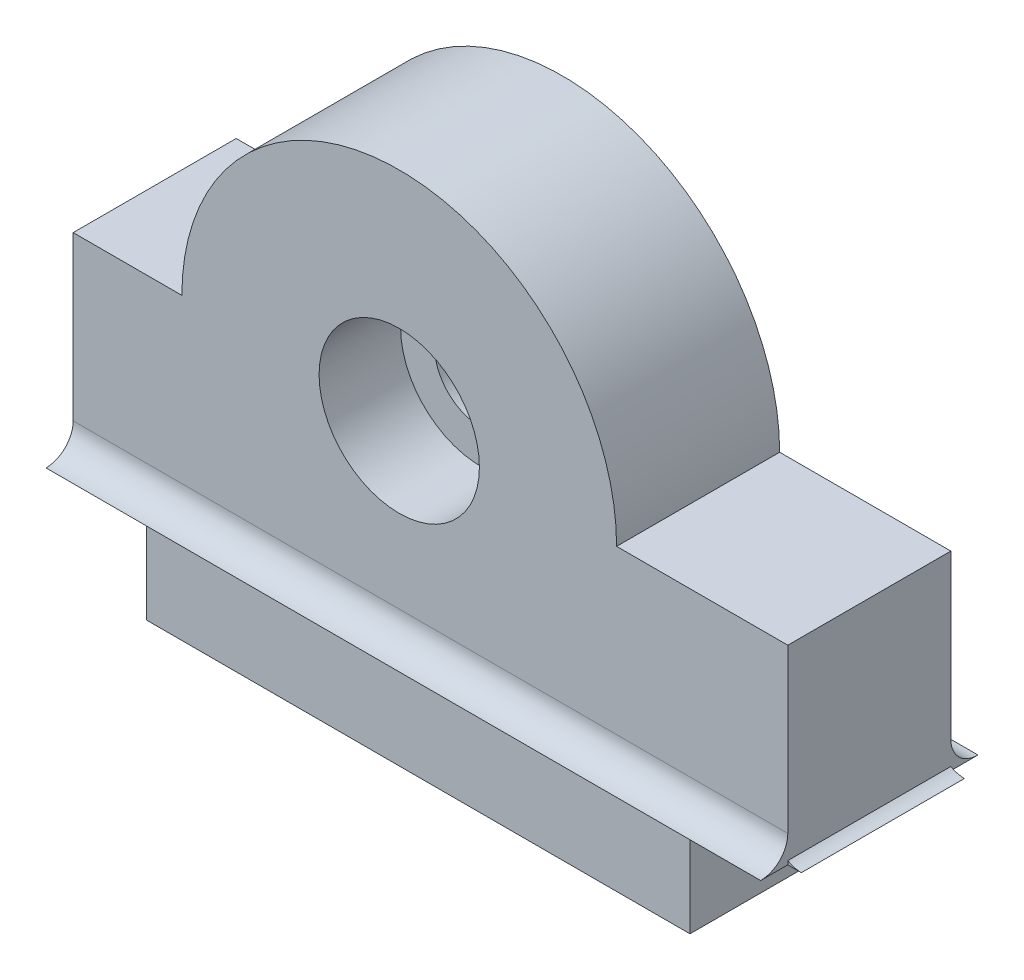
SolidWorks part; units mm, degrees
ref_plane "Front Plane" through (0, 0, 0) normal (0, 0, 1) x (1, 0, 0)
ref_plane "Top Plane" through (0, 0, 0) normal (0, 1, 0) x (1, 0, 0)
ref_plane "Right Plane" through (0, 0, 0) normal (1, 0, 0) x (0, 0, -1)
sketch "Sketch1" plane through (0, 0, 0) normal (0, 0, 1) x (1, 0, 0)
  line L0 (0, 0) -> (20, 0)
  line L1 (0, 0) -> (0, 4)
  line L2 (20, 0) -> (20, 4)
  line L3 (0, 4) -> (-2.7, 4)
  line L4 (23.6, 11) -> (23.6, 4)
  line L5 (-2.7, 4) -> (-2.7, 11)
  line L6 (-2.7, 11) -> (1.3, 11)
  line L7 (17.3, 11) -> (23.6, 11)
  line L8 (23.6, 4) -> (20, 4)
  line L9 (1.3, 11) -> (9.3, 11) construction
  line L10 (12.9373, 11) -> (9.3, 11) construction
  arc A0 (17.3, 11) -> (1.3, 11) centre (9.3, 11) ccw
  circle A1 centre (9.3, 11) radius 2.95
  point P19 (10, 0)
  point P22 (9.3, 11)
  dimension "D1" = 7
  dimension "D5" = 9.3
  dimension "D6" = 20
  dimension "D2" = 8
  dimension "D4" = 5.9
  dimension "D3" = 2.7
  dimension "D7" = 23.6
  dimension "D9" = 4
extrude "Boss-Extrude1" add sketch "Sketch1" along normal blind 6
sketch "Sketch2" plane through (-2.7, 0, 0) normal (-1, 0, 0) x (0, 0, 1)
  line L0 (3, 0) -> (3, 7) construction
  line L1 (6, 4) -> (6, 5)
  line L2 (6, 4) -> (7, 4)
  line L3 (0, 4) -> (-1, 4)
  line L4 (0, 4) -> (0, 5)
  arc A0 (6, 5) -> (7, 4) centre (7, 5) ccw
  arc A1 (0, 5) -> (-1, 4) centre (-1, 5) cw
  dimension "D1" = 1
  dimension "D2" = 1
  dimension "D3" = 6
  dimension "D4" = 3
  dimension "D5" = 4
extrude "Boss-Extrude2" add sketch "Sketch2" against normal up to surface (26.3 mm away) up to face at (23.6, 7.5, 3)
sketch "Sketch4" plane through (0, 0, 6) normal (0, 0, 1) x (1, 0, 0)
  line L0 (10.8, 0) -> (10.8, 7) construction
  line L1 (23.1, 4) -> (23.1, 5)
  line L2 (23.1, 4) -> (24.1, 4)
  line L3 (-1.5, 4) -> (-2.5, 4)
  line L4 (-1.5, 4) -> (-1.5, 5)
  arc A0 (23.1, 5) -> (24.1, 4) centre (24.1, 5) ccw
  arc A1 (-1.5, 5) -> (-2.5, 4) centre (-2.5, 5) cw
  dimension "D1" = 1
  dimension "D2" = 1
  dimension "D3" = 10.8
  dimension "D4" = 12.3
  dimension "D5" = 4
extrude "Boss-Extrude3" add sketch "Sketch4" against normal up to surface (6 mm away) up to face at (12.25, 11, 0)
sketch "Sketch5" plane through (0, 0, 0) normal (0, 0, -1) x (-1, 0, 0)
  line L0 (-9.3, 13.95) -> (-9.3, 8.05) construction
  circle A0 centre (-9.3, 11) radius 2.95 construction
  circle A1 centre (-9.3, 11) radius 1.7
  circle A2 centre (-9.3, 11) radius 2.95
  dimension "D1" = 3.4
  dimension "D2" = 5.9
extrude "Boss-Extrude4" add sketch "Sketch5" against normal blind 3
equation "\"D4@Sketch1\"= 5.5 + \"tol1@parametersSketch@prostheticParameters.SLDPRT\""
equation "\"D1@Sketch5\"= 3 + \"tol1@parametersSketch@prostheticParameters.SLDPRT\""
equation "\"D2@Sketch5\"= 5.5 + \"tol1@parametersSketch@prostheticParameters.SLDPRT\""
